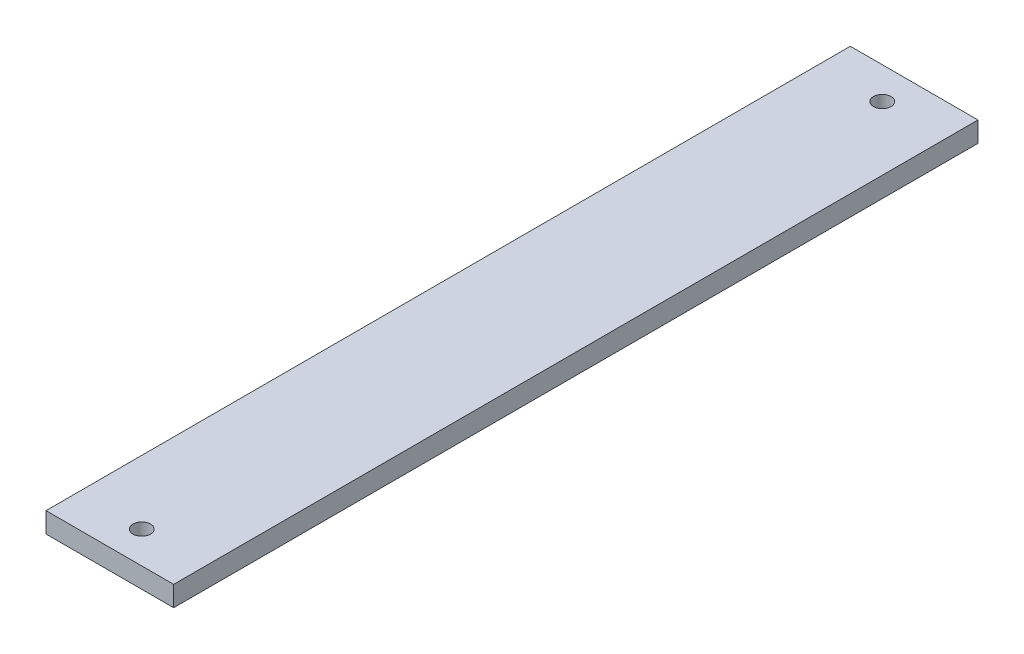
SolidWorks part; units mm, degrees
material "PA Type 6"
ref_plane "Front Plane" through (0, 0, 0) normal (0, 0, 1) x (1, 0, 0)
ref_plane "Top Plane" through (0, 0, 0) normal (0, 1, 0) x (1, 0, 0)
ref_plane "Right Plane" through (0, 0, 0) normal (1, 0, 0) x (0, 0, -1)
sketch "Sketch1" plane through (0, 0, 0) normal (0, 1, 0) x (1, 0, 0)
  line L0 (0, 0) -> (0, 116) construction
  line L1 (-20, -126) -> (20, -126)
  line L2 (-20, -126) -> (-20, 126)
  line L3 (-20, 126) -> (20, 126)
  line L4 (20, -126) -> (20, 126)
  line L5 (-20, -126) -> (20, 126) construction
  line L6 (-20, 126) -> (20, -126) construction
  line L7 (0, 0) -> (0, -116) construction
  circle A0 centre (0, 116) radius 2.75
  circle A1 centre (0, -116) radius 2.75
  point P0 (0, 0)
  dimension "D3" = 5.5
  dimension "D1" = 40
  dimension "D2" = 252
  dimension "D4" = 10
extrude "Boss-Extrude1" add sketch "Sketch1" along normal blind 6.35 contours L1 L4 L3 L2 A1 A0
